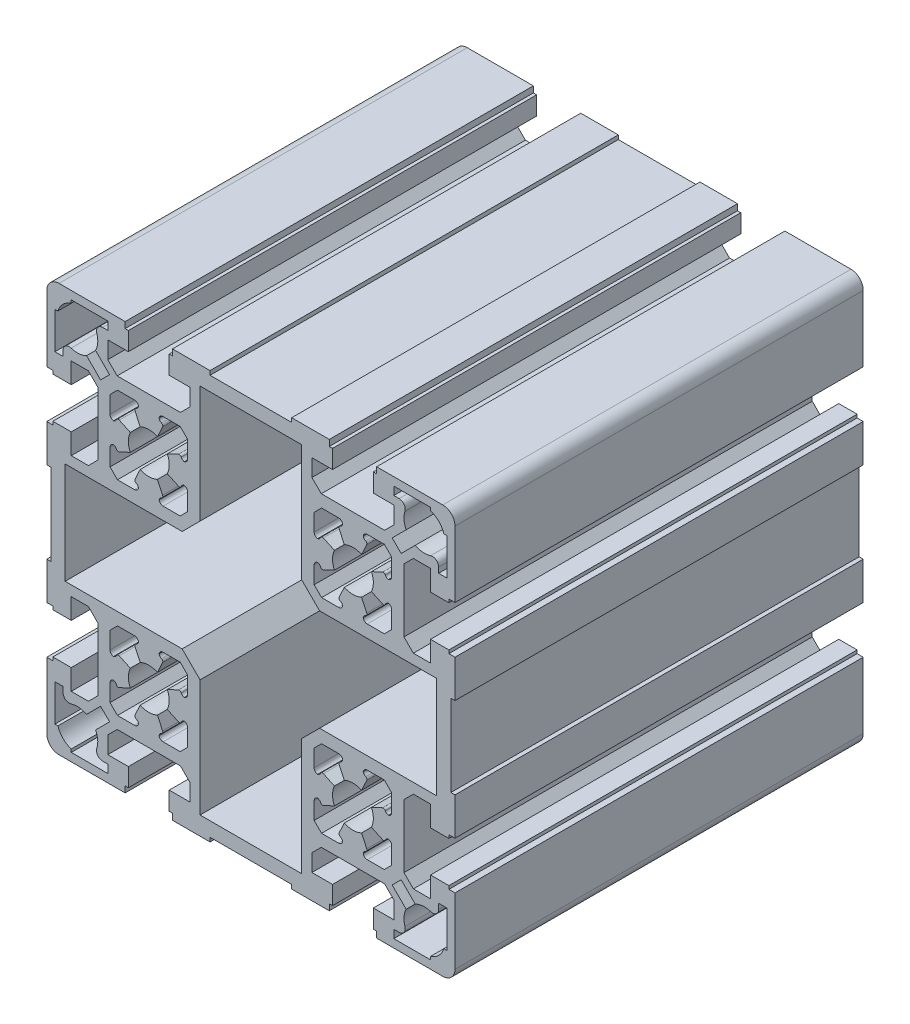
SolidWorks part; units mm, degrees
ref_plane "Front Plane" through (0, 0, 0) normal (0, 0, 1) x (1, 0, 0)
ref_plane "Top Plane" through (0, 0, 0) normal (0, 1, 0) x (1, 0, 0)
ref_plane "Right Plane" through (0, 0, 0) normal (1, 0, 0) x (0, 0, -1)
sketch "Sketch1" plane through (0, 0, 0) normal (0, 0, 1) x (1, 0, 0)
  line L0 (-15.5014, -32.6803) -> (-17.3205, -34.4994)
  line L1 (-12.45, -16.8336) -> (-16.8336, -12.45)
  line L2 (-17.25, -37.5) -> (-14.95, -39.8)
  line L3 (-14.95, -44) -> (-20, -44)
  line L4 (-19.2, -50) -> (-10, -50)
  line L5 (-35.05, -44) -> (-35.05, -39.8)
  line L6 (-50, -30.8) -> (-50, -47)
  line L7 (-48, -44) -> (-48, -35)
  line L8 (-47, -50) -> (-30.8, -50)
  line L9 (-35, -48) -> (-44, -48)
  line L10 (-44, -48) -> (-44, -47.2697)
  line L11 (-47.2697, -44) -> (-48, -44)
  line L12 (-20, -44) -> (-20, -48.5)
  line L13 (-30, -48.5) -> (-30, -44)
  line L14 (-35, -46) -> (-35, -48)
  line L15 (-30.8, -50) -> (-30.8, -48.5)
  line L16 (-30.8, -48.5) -> (-30, -48.5)
  line L17 (-20, -48.5) -> (-19.2, -48.5)
  line L18 (-19.2, -48.5) -> (-19.2, -50)
  line L19 (-30, -44) -> (-35.05, -44)
  line L20 (-36.3153, -46) -> (-35, -46)
  line L21 (-22.8883, -20.4679) -> (-21.6205, -17.7489)
  line L22 (-28.3809, -17.7495) -> (-27.1136, -20.4674)
  line L23 (-34.5, -21.5) -> (-34.5, -17.3191)
  line L24 (-44, -20) -> (-44, -14.95)
  line L25 (-50, -10) -> (-50, -19.2)
  line L26 (-37.5, -17.25) -> (-37.5, -32.75)
  line L27 (-21.6205, -32.2499) -> (-22.8883, -29.531)
  line L28 (-27.1145, -29.531) -> (-28.3824, -32.2499)
  line L29 (-34.5014, -32.6803) -> (-34.5014, -28.4994)
  line L30 (-37.5, -32.75) -> (-39.8, -35.05)
  line L31 (-40.2429, -38.0385) -> (-36.814, -34.6096)
  line L32 (-34.6096, -36.814) -> (-38.0385, -40.2429)
  line L33 (-46, -35) -> (-46, -36.3153)
  line L34 (-44, -30) -> (-48.5, -30)
  line L35 (-48.5, -30) -> (-48.5, -30.8)
  line L36 (-48.5, -30.8) -> (-50, -30.8)
  line L37 (-39.8, -35.05) -> (-44, -35.05)
  line L38 (-44, -35.05) -> (-44, -30)
  line L39 (-48, -35) -> (-46, -35)
  line L40 (-36.814, -34.6096) -> (-34.6096, -36.814)
  line L41 (-32.75, -37.5) -> (-17.25, -37.5)
  line L42 (-35.05, -39.8) -> (-32.75, -37.5)
  line L43 (-28.1405, -32.9143) -> (-28.0788, -32.9431)
  line L44 (-28.5014, -34.4994) -> (-32.6823, -34.4994)
  line L45 (-32.6823, -34.4994) -> (-34.5014, -32.6803)
  line L46 (-17.3205, -34.4994) -> (-21.5014, -34.4994)
  line L47 (-21.924, -32.9431) -> (-21.8623, -32.9143)
  line L48 (-48.5, -20) -> (-44, -20)
  line L49 (-50, -19.2) -> (-48.5, -19.2)
  line L50 (-48.5, -19.2) -> (-48.5, -20)
  line L51 (-32.9451, -28.0768) -> (-32.9164, -28.1385)
  line L52 (-32.2519, -28.3804) -> (-29.533, -27.1125)
  line L53 (-20.4699, -27.1125) -> (-17.751, -28.3804)
  line L54 (-17.0865, -28.1385) -> (-17.0577, -28.0768)
  line L55 (-29.533, -22.8863) -> (-32.2519, -21.6185)
  line L56 (-32.9164, -21.8603) -> (-32.9437, -21.9226)
  line L57 (-17.0577, -21.922) -> (-17.0865, -21.8603)
  line L58 (-17.751, -21.6185) -> (-20.4699, -22.8863)
  line L59 (-39.8, -14.95) -> (-37.5, -17.25)
  line L60 (-16.8336, -12.45) -> (-45.5, -12.45)
  line L61 (-44, -14.95) -> (-39.8, -14.95)
  line L62 (-49, -10) -> (-50, -10)
  line L63 (-28.0774, -17.0563) -> (-28.1391, -17.0851)
  line L64 (-34.5, -17.3191) -> (-32.6809, -15.5)
  line L65 (-32.6809, -15.5) -> (-28.5, -15.5)
  line L66 (-21.8623, -17.0845) -> (-21.924, -17.0557)
  line L67 (-21.5014, -15.4994) -> (-17.3205, -15.4994)
  line L68 (50, -47) -> (50, -30.8)
  line L69 (48, -35) -> (48, -44)
  line L70 (35.05, -39.8) -> (35.05, -44)
  line L71 (14.95, -44) -> (14.95, -39.8)
  line L72 (12.45, -16.8336) -> (12.45, -45.5)
  line L73 (-14.95, -39.8) -> (-14.95, -44)
  line L74 (-12.45, -45.5) -> (-12.45, -16.8336)
  line L75 (12.45, -45.5) -> (-12.45, -45.5)
  line L76 (-10, -49) -> (10, -49)
  line L77 (-10, -50) -> (-10, -49)
  line L78 (20, -48.5) -> (20, -44)
  line L79 (10, -50) -> (19.2, -50)
  line L80 (10, -49) -> (10, -50)
  line L81 (19.2, -50) -> (19.2, -48.5)
  line L82 (19.2, -48.5) -> (20, -48.5)
  line L83 (20, -44) -> (14.95, -44)
  line L84 (30, -44) -> (30, -48.5)
  line L85 (35, -48) -> (35, -46)
  line L86 (30.8, -50) -> (47, -50)
  line L87 (44, -48) -> (35, -48)
  line L88 (30, -48.5) -> (30.8, -48.5)
  line L89 (30.8, -48.5) -> (30.8, -50)
  line L90 (44, -47.2697) -> (44, -48)
  line L91 (35.05, -44) -> (30, -44)
  line L92 (35, -46) -> (36.3153, -46)
  line L93 (48, -44) -> (47.2697, -44)
  line L94 (50, -19.2) -> (50, -10)
  line L95 (44, -14.95) -> (44, -20)
  line L96 (34.5, -17.3191) -> (34.5, -21.5)
  line L97 (37.5, -32.75) -> (37.5, -17.25)
  line L98 (21.6191, -17.7495) -> (22.8869, -20.4685)
  line L99 (27.1131, -20.4685) -> (28.3809, -17.7495)
  line L100 (15.5, -21.5) -> (15.5, -17.3191)
  line L101 (-15.5014, -17.3185) -> (-15.5014, -21.4994)
  line L102 (28.3809, -32.2505) -> (27.1131, -29.5315)
  line L103 (17.25, -37.5) -> (32.75, -37.5)
  line L104 (22.8869, -29.5315) -> (21.6191, -32.2505)
  line L105 (15.5, -32.6809) -> (15.5, -28.5)
  line L106 (-15.5014, -28.4994) -> (-15.5014, -32.6803)
  line L107 (14.95, -39.8) -> (17.25, -37.5)
  line L108 (17.3191, -34.5) -> (15.5, -32.6809)
  line L109 (21.8609, -32.9149) -> (21.9226, -32.9437)
  line L110 (21.5, -34.5) -> (17.3191, -34.5)
  line L111 (17.7495, -28.3809) -> (20.4685, -27.1131)
  line L112 (17.0563, -28.0774) -> (17.0851, -28.1391)
  line L113 (20.4685, -22.8869) -> (17.7495, -21.6191)
  line L114 (17.0851, -21.8609) -> (17.0563, -21.9226)
  line L115 (34.5, -28.5) -> (34.5, -32.6809)
  line L116 (50, -30.8) -> (48.5, -30.8)
  line L117 (46, -36.3153) -> (46, -35)
  line L118 (34.6096, -36.814) -> (36.814, -34.6096)
  line L119 (36.814, -34.6096) -> (40.2429, -38.0385)
  line L120 (32.75, -37.5) -> (35.05, -39.8)
  line L121 (38.0385, -40.2429) -> (34.6096, -36.814)
  line L122 (39.8, -35.05) -> (37.5, -32.75)
  line L123 (34.5, -32.6809) -> (32.6809, -34.5)
  line L124 (32.6809, -34.5) -> (28.5, -34.5)
  line L125 (28.0774, -32.9437) -> (28.1391, -32.9149)
  line L126 (48.5, -30.8) -> (48.5, -30)
  line L127 (44, -30) -> (44, -35.05)
  line L128 (44, -35.05) -> (39.8, -35.05)
  line L129 (48.5, -30) -> (44, -30)
  line L130 (46, -35) -> (48, -35)
  line L131 (48.5, -19.2) -> (50, -19.2)
  line L132 (29.5315, -27.1131) -> (32.2505, -28.3809)
  line L133 (32.9149, -28.1391) -> (32.9437, -28.0774)
  line L134 (32.9437, -21.9226) -> (32.9149, -21.8609)
  line L135 (32.2505, -21.6191) -> (29.5315, -22.8869)
  line L136 (48.5, -20) -> (48.5, -19.2)
  line L137 (44, -20) -> (48.5, -20)
  line L138 (45.5, -12.45) -> (16.8336, -12.45)
  line L139 (15.5, -17.3191) -> (17.3191, -15.5)
  line L140 (16.8336, -12.45) -> (12.45, -16.8336)
  line L141 (21.9226, -17.0563) -> (21.8609, -17.0851)
  line L142 (17.3191, -15.5) -> (21.5, -15.5)
  line L143 (50, -10) -> (49, -10)
  line L144 (37.5, -17.25) -> (39.8, -14.95)
  line L145 (28.5, -15.5) -> (32.6809, -15.5)
  line L146 (32.6809, -15.5) -> (34.5, -17.3191)
  line L147 (28.1391, -17.0851) -> (28.0774, -17.0563)
  line L148 (39.8, -14.95) -> (44, -14.95)
  line L149 (-17.3191, 34.5) -> (-15.5, 32.6809)
  line L150 (-15.5, 17.3191) -> (-17.3191, 15.5)
  line L151 (-16.8336, 12.45) -> (-12.45, 16.8336)
  line L152 (-10, 50) -> (-19.2, 50)
  line L153 (-20, 44) -> (-14.95, 44)
  line L154 (-14.95, 39.8) -> (-17.25, 37.5)
  line L155 (-37.5, 32.75) -> (-37.5, 17.25)
  line L156 (-32.6809, 15.5) -> (-34.5, 17.3191)
  line L157 (-37.5, 17.25) -> (-39.8, 14.95)
  line L158 (-44, 14.95) -> (-44, 20)
  line L159 (-50, 19.2) -> (-50, 10)
  line L160 (-45.5, 12.45) -> (-16.8336, 12.45)
  line L161 (-50, 10) -> (-49, 10)
  line L162 (-39.8, 14.95) -> (-44, 14.95)
  line L163 (-28.5, 15.5) -> (-32.6809, 15.5)
  line L164 (-17.3191, 15.5) -> (-21.5, 15.5)
  line L165 (-44, 20) -> (-48.5, 20)
  line L166 (-48.5, 20) -> (-48.5, 19.2)
  line L167 (-48.5, 19.2) -> (-50, 19.2)
  line L168 (-20.4685, 22.8869) -> (-17.7495, 21.6191)
  line L169 (-32.2505, 21.6191) -> (-29.5315, 22.8869)
  line L170 (-34.5, 17.3191) -> (-34.5, 21.5)
  line L171 (-32.9437, 21.9226) -> (-32.9149, 21.8609)
  line L172 (-27.1131, 20.4685) -> (-28.3809, 17.7495)
  line L173 (-28.1391, 17.0851) -> (-28.0774, 17.0563)
  line L174 (-17.0851, 21.8609) -> (-17.0563, 21.9226)
  line L175 (-21.9226, 17.0563) -> (-21.8609, 17.0851)
  line L176 (-21.6191, 17.7495) -> (-22.8869, 20.4685)
  line L177 (-29.5315, 27.1131) -> (-32.2505, 28.3809)
  line L178 (-32.9149, 28.1391) -> (-32.9437, 28.0774)
  line L179 (-17.0563, 28.0774) -> (-17.0851, 28.1391)
  line L180 (-17.7495, 28.3809) -> (-20.4685, 27.1131)
  line L181 (-35.05, 39.8) -> (-35.05, 44)
  line L182 (-50, 47) -> (-50, 30.8)
  line L183 (-48, 35) -> (-48, 44)
  line L184 (-38.0385, 40.2429) -> (-34.6096, 36.814)
  line L185 (-39.8, 35.05) -> (-37.5, 32.75)
  line L186 (-36.814, 34.6096) -> (-40.2429, 38.0385)
  line L187 (-44, 30) -> (-44, 35.05)
  line L188 (-48.5, 30) -> (-44, 30)
  line L189 (-50, 30.8) -> (-48.5, 30.8)
  line L190 (-48.5, 30.8) -> (-48.5, 30)
  line L191 (-44, 35.05) -> (-39.8, 35.05)
  line L192 (-46, 36.3153) -> (-46, 35)
  line L193 (-46, 35) -> (-48, 35)
  line L194 (-34.5, 32.6809) -> (-32.6809, 34.5)
  line L195 (-34.5, 28.5) -> (-34.5, 32.6809)
  line L196 (-28.0774, 32.9437) -> (-28.1397, 32.9164)
  line L197 (-28.3815, 32.2519) -> (-27.113, 29.5316)
  line L198 (-22.8869, 29.5315) -> (-21.6191, 32.2505)
  line L199 (-21.8609, 32.9149) -> (-21.9226, 32.9437)
  line L200 (-17.25, 37.5) -> (-32.75, 37.5)
  line L201 (-32.75, 37.5) -> (-35.05, 39.8)
  line L202 (-32.6809, 34.5) -> (-28.5, 34.5)
  line L203 (-34.6096, 36.814) -> (-36.814, 34.6096)
  line L204 (-21.5, 34.5) -> (-17.3191, 34.5)
  line L205 (-30.8, 50) -> (-47, 50)
  line L206 (-44, 48) -> (-35, 48)
  line L207 (-48, 44) -> (-47.2697, 44)
  line L208 (-44, 47.2697) -> (-44, 48)
  line L209 (-20, 48.5) -> (-20, 44)
  line L210 (-30, 44) -> (-30, 48.5)
  line L211 (-35.05, 44) -> (-30, 44)
  line L212 (-30, 48.5) -> (-30.8, 48.5)
  line L213 (-30.8, 48.5) -> (-30.8, 50)
  line L214 (-35, 48) -> (-35, 46)
  line L215 (-35, 46) -> (-36.3153, 46)
  line L216 (-19.2, 50) -> (-19.2, 48.5)
  line L217 (-19.2, 48.5) -> (-20, 48.5)
  line L218 (37.5, 17.25) -> (37.5, 32.75)
  line L219 (12.45, 45.5) -> (12.45, 16.8336)
  line L220 (-12.45, 16.8336) -> (-12.45, 45.5)
  line L221 (28.3809, 17.7495) -> (27.1131, 20.4685)
  line L222 (16.8336, 12.45) -> (45.5, 12.45)
  line L223 (17.3191, 15.5) -> (15.5, 17.3191)
  line L224 (12.45, 16.8336) -> (16.8336, 12.45)
  line L225 (21.5, 15.5) -> (17.3191, 15.5)
  line L226 (-15.5, 21.5) -> (-15.5, 17.3191)
  line L227 (17.7495, 21.6191) -> (20.4685, 22.8869)
  line L228 (15.5, 17.3191) -> (15.5, 21.5)
  line L229 (22.8869, 20.4685) -> (21.6191, 17.7495)
  line L230 (21.8609, 17.0851) -> (21.9226, 17.0563)
  line L231 (17.0563, 21.9226) -> (17.0851, 21.8609)
  line L232 (20.4685, 27.1131) -> (17.7495, 28.3809)
  line L233 (17.0851, 28.1391) -> (17.0563, 28.0774)
  line L234 (44, 20) -> (44, 14.95)
  line L235 (34.5, 17.3191) -> (32.6809, 15.5)
  line L236 (39.8, 14.95) -> (37.5, 17.25)
  line L237 (50, 10) -> (50, 19.2)
  line L238 (49, 10) -> (50, 10)
  line L239 (32.6809, 15.5) -> (28.5, 15.5)
  line L240 (44, 14.95) -> (39.8, 14.95)
  line L241 (50, 19.2) -> (48.5, 19.2)
  line L242 (29.5315, 22.8869) -> (32.2505, 21.6191)
  line L243 (32.9149, 21.8609) -> (32.9437, 21.9226)
  line L244 (34.5, 21.5) -> (34.5, 17.3191)
  line L245 (28.0774, 17.0563) -> (28.1391, 17.0851)
  line L246 (48.5, 19.2) -> (48.5, 20)
  line L247 (48.5, 20) -> (44, 20)
  line L248 (32.9431, 28.076) -> (32.9143, 28.1377)
  line L249 (32.2499, 28.3795) -> (29.532, 27.1121)
  line L250 (27.1131, 29.5315) -> (28.3809, 32.2505)
  line L251 (32.75, 37.5) -> (17.25, 37.5)
  line L252 (14.95, 39.8) -> (14.95, 44)
  line L253 (-14.95, 44) -> (-14.95, 39.8)
  line L254 (-15.5, 32.6809) -> (-15.5, 28.5)
  line L255 (15.5, 32.6809) -> (17.3191, 34.5)
  line L256 (15.5, 28.5) -> (15.5, 32.6809)
  line L257 (21.9226, 32.9437) -> (21.8603, 32.9164)
  line L258 (21.6185, 32.2519) -> (22.887, 29.5316)
  line L259 (17.25, 37.5) -> (14.95, 39.8)
  line L260 (17.3191, 34.5) -> (21.5, 34.5)
  line L261 (-12.45, 45.5) -> (12.45, 45.5)
  line L262 (10, 49) -> (-10, 49)
  line L263 (-10, 49) -> (-10, 50)
  line L264 (20, 44) -> (20, 48.5)
  line L265 (14.95, 44) -> (20, 44)
  line L266 (19.2, 50) -> (10, 50)
  line L267 (10, 50) -> (10, 49)
  line L268 (20, 48.5) -> (19.2, 48.5)
  line L269 (19.2, 48.5) -> (19.2, 50)
  line L270 (50, 30.8) -> (50, 47)
  line L271 (48, 44) -> (48, 35)
  line L272 (35.05, 44) -> (35.05, 39.8)
  line L273 (34.6096, 36.814) -> (38.0385, 40.2429)
  line L274 (48.5, 30.8) -> (50, 30.8)
  line L275 (44, 35.05) -> (44, 30)
  line L276 (32.6803, 34.4986) -> (34.4994, 32.6795)
  line L277 (37.5, 32.75) -> (39.8, 35.05)
  line L278 (34.4994, 32.6795) -> (34.4994, 28.4986)
  line L279 (28.1391, 32.9149) -> (28.0768, 32.9423)
  line L280 (48.5, 30) -> (48.5, 30.8)
  line L281 (44, 30) -> (48.5, 30)
  line L282 (40.2429, 38.0385) -> (36.814, 34.6096)
  line L283 (35.05, 39.8) -> (32.75, 37.5)
  line L284 (28.4994, 34.4986) -> (32.6803, 34.4986)
  line L285 (36.814, 34.6096) -> (34.6096, 36.814)
  line L286 (39.8, 35.05) -> (44, 35.05)
  line L287 (46, 35) -> (46, 36.3153)
  line L288 (48, 35) -> (46, 35)
  line L289 (30, 48.5) -> (30, 44)
  line L290 (30, 44) -> (35.05, 44)
  line L291 (47.2697, 44) -> (48, 44)
  line L292 (47, 50) -> (30.8, 50)
  line L293 (35, 48) -> (44, 48)
  line L294 (30.8, 50) -> (30.8, 48.5)
  line L295 (30.8, 48.5) -> (30, 48.5)
  line L296 (36.3153, 46) -> (35, 46)
  line L297 (35, 46) -> (35, 48)
  line L298 (44, 48) -> (44, 47.2697)
  line L299 (-49, 10) -> (-49, -10)
  line L300 (-45.5, 12.45) -> (-45.5, -12.45)
  line L301 (45.5, 12.45) -> (45.5, -12.45)
  line L302 (49, 10) -> (49, -10)
  line L303 (0, 53.1587) -> (0, -54.0147) construction
  line L304 (-52.9019, 0) -> (53.2443, 0) construction
  line L305 (-17.3205, -15.4994) -> (-15.5014, -17.3185)
  arc A0 (-16.3264, -22.484) -> (-15.5014, -21.4994) centre (-16.5014, -21.4994) ccw
  arc A1 (-15.5014, -28.4994) -> (-16.3264, -27.5148) centre (-16.5014, -28.4994) ccw
  arc A2 (-37.7426, -44.0385) -> (-38.0385, -40.2429) centre (-42.5, -42.5) ccw
  arc A3 (-37.7426, -44.0385) -> (-36.3153, -46) centre (-36.3153, -44.5) ccw
  arc A4 (-47.2697, -44) -> (-44, -47.2697) centre (-42.5, -42.5) ccw
  arc A5 (-50, -47) -> (-47, -50) centre (-47, -47) ccw
  arc A6 (-27.1145, -29.531) -> (-22.8883, -29.531) centre (-25.0014, -24.9994) ccw
  arc A7 (-46, -36.3153) -> (-44.0385, -37.7426) centre (-44.5, -36.3153) ccw
  arc A8 (-40.2429, -38.0385) -> (-44.0385, -37.7426) centre (-42.5, -42.5) ccw
  arc A9 (-28.3824, -32.2499) -> (-28.1405, -32.9143) centre (-27.9292, -32.4612) ccw
  arc A10 (-27.5169, -33.6744) -> (-28.0788, -32.9431) centre (-28.5014, -33.8494) ccw
  arc A11 (-28.5014, -34.4994) -> (-27.5169, -33.6744) centre (-28.5014, -33.4994) ccw
  arc A12 (-22.486, -33.6744) -> (-21.5014, -34.4994) centre (-21.5014, -33.4994) ccw
  arc A13 (-21.924, -32.9431) -> (-22.486, -33.6744) centre (-21.5014, -33.8494) ccw
  arc A14 (-21.8623, -32.9143) -> (-21.6205, -32.2499) centre (-22.0736, -32.4612) ccw
  arc A15 (-20.4699, -27.1125) -> (-20.4699, -22.8863) centre (-25.0014, -24.9994) ccw
  arc A16 (-29.533, -22.8863) -> (-29.533, -27.1125) centre (-25.0014, -24.9994) ccw
  arc A17 (-33.6764, -27.5148) -> (-34.5014, -28.4994) centre (-33.5014, -28.4994) ccw
  arc A18 (-32.9451, -28.0768) -> (-33.6764, -27.5148) centre (-33.8514, -28.4994) ccw
  arc A19 (-32.9164, -28.1385) -> (-32.2519, -28.3804) centre (-32.4632, -27.9272) ccw
  arc A20 (-17.751, -28.3804) -> (-17.0865, -28.1385) centre (-17.5397, -27.9272) ccw
  arc A21 (-16.3264, -27.5148) -> (-17.0577, -28.0768) centre (-16.1514, -28.4994) ccw
  arc A22 (-22.8883, -20.4679) -> (-27.1136, -20.4674) centre (-25.0014, -24.9994) ccw
  arc A23 (-32.2519, -21.6185) -> (-32.9164, -21.8603) centre (-32.4632, -22.0716) ccw
  arc A24 (-33.675, -22.4846) -> (-32.9437, -21.9226) centre (-33.85, -21.5) ccw
  arc A25 (-34.5, -21.5) -> (-33.675, -22.4846) centre (-33.5, -21.5) ccw
  arc A26 (-17.0577, -21.922) -> (-16.3264, -22.484) centre (-16.1514, -21.4994) ccw
  arc A27 (-17.0865, -21.8603) -> (-17.751, -21.6185) centre (-17.5397, -22.0716) ccw
  arc A28 (-28.0774, -17.0563) -> (-27.5154, -16.325) centre (-28.5, -16.15) ccw
  arc A29 (-28.1391, -17.0851) -> (-28.3809, -17.7495) centre (-27.9278, -17.5382) ccw
  arc A30 (-27.5154, -16.325) -> (-28.5, -15.5) centre (-28.5, -16.5) ccw
  arc A31 (-21.6205, -17.7489) -> (-21.8623, -17.0845) centre (-22.0736, -17.5376) ccw
  arc A32 (-22.486, -16.3244) -> (-21.924, -17.0557) centre (-21.5014, -16.1494) ccw
  arc A33 (-21.5014, -15.4994) -> (-22.486, -16.3244) centre (-21.5014, -16.4994) ccw
  arc A34 (38.0385, -40.2429) -> (37.7426, -44.0385) centre (42.5, -42.5) ccw
  arc A35 (47, -50) -> (50, -47) centre (47, -47) ccw
  arc A36 (44, -47.2697) -> (47.2697, -44) centre (42.5, -42.5) ccw
  arc A37 (36.3153, -46) -> (37.7426, -44.0385) centre (36.3153, -44.5) ccw
  arc A38 (28.0774, -32.9437) -> (27.5154, -33.675) centre (28.5, -33.85) ccw
  arc A39 (27.5154, -33.675) -> (28.5, -34.5) centre (28.5, -33.5) ccw
  arc A40 (22.8869, -29.5315) -> (27.1131, -29.5315) centre (25, -25) ccw
  arc A41 (21.6191, -32.2505) -> (21.8609, -32.9149) centre (22.0722, -32.4618) ccw
  arc A42 (22.4846, -33.675) -> (21.9226, -32.9437) centre (21.5, -33.85) ccw
  arc A43 (21.5, -34.5) -> (22.4846, -33.675) centre (21.5, -33.5) ccw
  arc A44 (20.4685, -22.8869) -> (20.4685, -27.1131) centre (25, -25) ccw
  arc A45 (17.0563, -28.0774) -> (16.325, -27.5154) centre (16.15, -28.5) ccw
  arc A46 (16.325, -27.5154) -> (15.5, -28.5) centre (16.5, -28.5) ccw
  arc A47 (17.0851, -28.1391) -> (17.7495, -28.3809) centre (17.5382, -27.9278) ccw
  arc A48 (16.325, -22.4846) -> (17.0563, -21.9226) centre (16.15, -21.5) ccw
  arc A49 (15.5, -21.5) -> (16.325, -22.4846) centre (16.5, -21.5) ccw
  arc A50 (27.1131, -20.4685) -> (22.8869, -20.4685) centre (25, -25) ccw
  arc A51 (17.7495, -21.6191) -> (17.0851, -21.8609) centre (17.5382, -22.0722) ccw
  arc A52 (44.0385, -37.7426) -> (40.2429, -38.0385) centre (42.5, -42.5) ccw
  arc A53 (44.0385, -37.7426) -> (46, -36.3153) centre (44.5, -36.3153) ccw
  arc A54 (28.1391, -32.9149) -> (28.3809, -32.2505) centre (27.9278, -32.4618) ccw
  arc A55 (29.5315, -27.1131) -> (29.5315, -22.8869) centre (25, -25) ccw
  arc A56 (32.2505, -28.3809) -> (32.9149, -28.1391) centre (32.4618, -27.9278) ccw
  arc A57 (33.675, -27.5154) -> (32.9437, -28.0774) centre (33.85, -28.5) ccw
  arc A58 (34.5, -28.5) -> (33.675, -27.5154) centre (33.5, -28.5) ccw
  arc A59 (33.675, -22.4846) -> (34.5, -21.5) centre (33.5, -21.5) ccw
  arc A60 (32.9437, -21.9226) -> (33.675, -22.4846) centre (33.85, -21.5) ccw
  arc A61 (32.9149, -21.8609) -> (32.2505, -21.6191) centre (32.4618, -22.0722) ccw
  arc A62 (27.5154, -16.325) -> (28.0774, -17.0563) centre (28.5, -16.15) ccw
  arc A63 (28.5, -15.5) -> (27.5154, -16.325) centre (28.5, -16.5) ccw
  arc A64 (22.4846, -16.325) -> (21.5, -15.5) centre (21.5, -16.5) ccw
  arc A65 (21.9226, -17.0563) -> (22.4846, -16.325) centre (21.5, -16.15) ccw
  arc A66 (21.8609, -17.0851) -> (21.6191, -17.7495) centre (22.0722, -17.5382) ccw
  arc A67 (28.3809, -17.7495) -> (28.1391, -17.0851) centre (27.9278, -17.5382) ccw
  arc A68 (-16.325, 27.5154) -> (-15.5, 28.5) centre (-16.5, 28.5) ccw
  arc A69 (-15.5, 21.5) -> (-16.325, 22.4846) centre (-16.5, 21.5) ccw
  arc A70 (-17.0851, 28.1391) -> (-17.7495, 28.3809) centre (-17.5382, 27.9278) ccw
  arc A71 (-32.2505, 28.3809) -> (-32.9149, 28.1391) centre (-32.4618, 27.9278) ccw
  arc A72 (-34.5, 28.5) -> (-33.675, 27.5154) centre (-33.5, 28.5) ccw
  arc A73 (-21.9226, 17.0563) -> (-22.4846, 16.325) centre (-21.5, 16.15) ccw
  arc A74 (-27.5154, 16.325) -> (-28.0774, 17.0563) centre (-28.5, 16.15) ccw
  arc A75 (-28.5, 15.5) -> (-27.5154, 16.325) centre (-28.5, 16.5) ccw
  arc A76 (-22.4846, 16.325) -> (-21.5, 15.5) centre (-21.5, 16.5) ccw
  arc A77 (-33.675, 22.4846) -> (-34.5, 21.5) centre (-33.5, 21.5) ccw
  arc A78 (-27.1131, 20.4685) -> (-22.8869, 20.4685) centre (-25, 25) ccw
  arc A79 (-32.9437, 21.9226) -> (-33.675, 22.4846) centre (-33.85, 21.5) ccw
  arc A80 (-32.9149, 21.8609) -> (-32.2505, 21.6191) centre (-32.4618, 22.0722) ccw
  arc A81 (-28.3809, 17.7495) -> (-28.1391, 17.0851) centre (-27.9278, 17.5382) ccw
  arc A82 (-17.7495, 21.6191) -> (-17.0851, 21.8609) centre (-17.5382, 22.0722) ccw
  arc A83 (-16.325, 22.4846) -> (-17.0563, 21.9226) centre (-16.15, 21.5) ccw
  arc A84 (-21.8609, 17.0851) -> (-21.6191, 17.7495) centre (-22.0722, 17.5382) ccw
  arc A85 (-29.5315, 27.1131) -> (-29.5315, 22.8869) centre (-25, 25) ccw
  arc A86 (-33.675, 27.5154) -> (-32.9437, 28.0774) centre (-33.85, 28.5) ccw
  arc A87 (-17.0563, 28.0774) -> (-16.325, 27.5154) centre (-16.15, 28.5) ccw
  arc A88 (-20.4685, 22.8869) -> (-20.4685, 27.1131) centre (-25, 25) ccw
  arc A89 (-44.0385, 37.7426) -> (-40.2429, 38.0385) centre (-42.5, 42.5) ccw
  arc A90 (-44.0385, 37.7426) -> (-46, 36.3153) centre (-44.5, 36.3153) ccw
  arc A91 (-21.5, 34.5) -> (-22.4846, 33.675) centre (-21.5, 33.5) ccw
  arc A92 (-27.5154, 33.675) -> (-28.5, 34.5) centre (-28.5, 33.5) ccw
  arc A93 (-22.8869, 29.5315) -> (-27.113, 29.5316) centre (-25, 25) ccw
  arc A94 (-28.0774, 32.9437) -> (-27.5154, 33.675) centre (-28.5, 33.85) ccw
  arc A95 (-28.1397, 32.9164) -> (-28.3815, 32.2519) centre (-27.9284, 32.4632) ccw
  arc A96 (-21.6191, 32.2505) -> (-21.8609, 32.9149) centre (-22.0722, 32.4618) ccw
  arc A97 (-22.4846, 33.675) -> (-21.9226, 32.9437) centre (-21.5, 33.85) ccw
  arc A98 (-38.0385, 40.2429) -> (-37.7426, 44.0385) centre (-42.5, 42.5) ccw
  arc A99 (-36.3153, 46) -> (-37.7426, 44.0385) centre (-36.3153, 44.5) ccw
  arc A100 (-44, 47.2697) -> (-47.2697, 44) centre (-42.5, 42.5) ccw
  arc A101 (-47, 50) -> (-50, 47) centre (-47, 47) ccw
  arc A102 (33.6744, 27.514) -> (34.4994, 28.4986) centre (33.4994, 28.4986) ccw
  arc A103 (32.9143, 28.1377) -> (32.2499, 28.3795) centre (32.4612, 27.9264) ccw
  arc A104 (15.5, 28.5) -> (16.325, 27.5154) centre (16.5, 28.5) ccw
  arc A105 (17.7495, 28.3809) -> (17.0851, 28.1391) centre (17.5382, 27.9278) ccw
  arc A106 (28.0774, 17.0563) -> (27.5154, 16.325) centre (28.5, 16.15) ccw
  arc A107 (27.5154, 16.325) -> (28.5, 15.5) centre (28.5, 16.5) ccw
  arc A108 (22.4846, 16.325) -> (21.9226, 17.0563) centre (21.5, 16.15) ccw
  arc A109 (21.5, 15.5) -> (22.4846, 16.325) centre (21.5, 16.5) ccw
  arc A110 (16.325, 22.4846) -> (15.5, 21.5) centre (16.5, 21.5) ccw
  arc A111 (17.0563, 21.9226) -> (16.325, 22.4846) centre (16.15, 21.5) ccw
  arc A112 (22.8869, 20.4685) -> (27.1131, 20.4685) centre (25, 25) ccw
  arc A113 (21.6191, 17.7495) -> (21.8609, 17.0851) centre (22.0722, 17.5382) ccw
  arc A114 (17.0851, 21.8609) -> (17.7495, 21.6191) centre (17.5382, 22.0722) ccw
  arc A115 (16.325, 27.5154) -> (17.0563, 28.0774) centre (16.15, 28.5) ccw
  arc A116 (20.4685, 27.1131) -> (20.4685, 22.8869) centre (25, 25) ccw
  arc A117 (34.5, 21.5) -> (33.675, 22.4846) centre (33.5, 21.5) ccw
  arc A118 (32.2505, 21.6191) -> (32.9149, 21.8609) centre (32.4618, 22.0722) ccw
  arc A119 (33.675, 22.4846) -> (32.9437, 21.9226) centre (33.85, 21.5) ccw
  arc A120 (28.1391, 17.0851) -> (28.3809, 17.7495) centre (27.9278, 17.5382) ccw
  arc A121 (32.9431, 28.076) -> (33.6744, 27.514) centre (33.8494, 28.4986) ccw
  arc A122 (29.5315, 22.8869) -> (29.532, 27.1121) centre (25, 25) ccw
  arc A123 (27.5148, 33.6736) -> (28.0768, 32.9423) centre (28.4994, 33.8486) ccw
  arc A124 (28.4994, 34.4986) -> (27.5148, 33.6736) centre (28.4994, 33.4986) ccw
  arc A125 (22.4846, 33.675) -> (21.5, 34.5) centre (21.5, 33.5) ccw
  arc A126 (21.9226, 32.9437) -> (22.4846, 33.675) centre (21.5, 33.85) ccw
  arc A127 (21.8603, 32.9164) -> (21.6185, 32.2519) centre (22.0716, 32.4632) ccw
  arc A128 (27.1131, 29.5315) -> (22.887, 29.5316) centre (25, 25) ccw
  arc A129 (28.3809, 32.2505) -> (28.1391, 32.9149) centre (27.9278, 32.4618) ccw
  arc A130 (46, 36.3153) -> (44.0385, 37.7426) centre (44.5, 36.3153) ccw
  arc A131 (40.2429, 38.0385) -> (44.0385, 37.7426) centre (42.5, 42.5) ccw
  arc A132 (50, 47) -> (47, 50) centre (47, 47) ccw
  arc A133 (47.2697, 44) -> (44, 47.2697) centre (42.5, 42.5) ccw
  arc A134 (37.7426, 44.0385) -> (36.3153, 46) centre (36.3153, 44.5) ccw
  arc A135 (37.7426, 44.0385) -> (38.0385, 40.2429) centre (42.5, 42.5) ccw
  dimension "D3" = 10
  dimension "D4" = 10
  dimension "D6" = 10
  dimension "D1" = 100
  dimension "D2" = 100
extrude "Base-Extrude" add sketch "Sketch1" against normal blind 100
